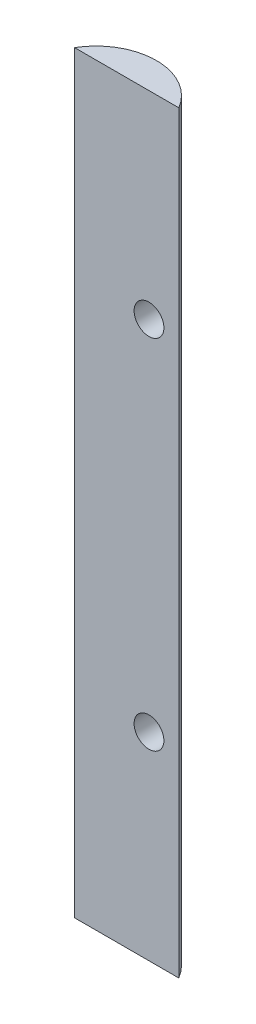
SolidWorks part; units mm, degrees
ref_plane "Front Plane" through (0, 0, 0) normal (0, 0, 1) x (1, 0, 0)
ref_plane "Top Plane" through (0, 0, 0) normal (0, 1, 0) x (1, 0, 0)
ref_plane "Right Plane" through (0, 0, 0) normal (1, 0, 0) x (0, 0, -1)
sketch "Sketch2" plane through (0, 0, 0) normal (0, 1, 0) x (1, 0, 0)
  line L2 (0, 0) -> (6.35, 0)
  line L3 (0, 0) -> (-15.875, 0)
  arc A2 (-15.875, 0) -> (6.35, 0) centre (-4.7625, -6.5484) cw
  point P4 (0, 0)
  point P7 (-4.7625, 6.35)
  dimension "D1" = 6.35
  dimension "D2" = 15.875
  dimension "D3" = 6.35
extrude "Boss-Extrude1" add sketch "Sketch2" along normal blind 160.652 from offset 6.35 offset against normal yes
sketch "Sketch1" plane through (0, 0, 0) normal (0, 0, 1) x (1, 0, 0)
  line L0 (0, -6.35) -> (0, 154.302) construction
  line L1 (-15.875, -6.35) -> (6.35, -6.35) construction
  line L2 (-15.875, 154.302) -> (6.35, 154.302) construction
  line L3 (0, 35.876) -> (0, 112.076) construction
  circle A2 centre (0, 35.876) radius 3.175
  circle A3 centre (0, 112.076) radius 3.175
  point P4 (0, 104.6713)
  point P12 (0, 140.1284)
  point P13 (0, 73.976)
  point P14 (0, 73.976)
  dimension "D1" = 6.35
  dimension "D2" = 76.2
extrude "Cut-Extrude2" cut sketch "Sketch1" against normal through all both
